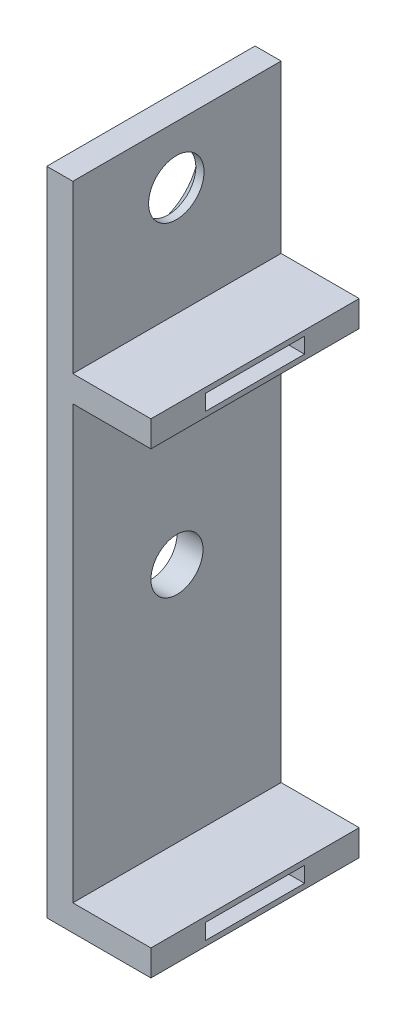
SolidWorks part; units mm, degrees
ref_plane "Front Plane" through (0, 0, 0) normal (0, 0, 1) x (1, 0, 0)
ref_plane "Top Plane" through (0, 0, 0) normal (0, 1, 0) x (1, 0, 0)
ref_plane "Right Plane" through (0, 0, 0) normal (1, 0, 0) x (0, 0, -1)
sketch "Sketch1" plane through (0, 0, 0) normal (0, 0, 1) x (1, 0, 0)
  line L0 (-22.4832, 11.6395) -> (-22.4832, -18.8404)
  line L1 (-22.4832, -18.8404) -> (-18.6732, -18.8404)
  line L2 (-18.6732, -18.8404) -> (-18.6732, -20.1105)
  line L3 (-18.6732, -20.1105) -> (-23.7532, -20.1105)
  line L4 (-23.7532, -20.1105) -> (-23.7532, 11.6395)
  line L5 (-23.7532, 11.6395) -> (-22.4832, 11.6395)
  dimension "D1" = 30.48
  dimension "D2" = 31.75
  dimension "D3" = 5.08
extrude "Boss-Extrude1" add sketch "Sketch1" along normal blind 10.16
sketch "Sketch5" plane through (-18.6732, 0, 0) normal (1, 0, 0) x (0, 0, -1)
  line L0 (-7.493, -19.8565) -> (-2.667, -19.8565)
  line L1 (-2.667, -19.8565) -> (-2.667, -19.0944)
  line L2 (-2.667, -19.0944) -> (-7.493, -19.0944)
  line L3 (-7.493, -19.0944) -> (-7.493, -19.8565)
  line L4 (0, -20.1105) -> (0, -18.8404) construction
  line L5 (-10.16, -20.1105) -> (-10.16, -18.8404) construction
  line L6 (-10.16, -18.8404) -> (0, -18.8404) construction
  line L7 (-10.16, -20.1105) -> (0, -20.1105) construction
  dimension "D1" = 2.667
  dimension "D2" = 2.667
  dimension "D3" = 0.254
  dimension "D4" = 0.254
sketch "Sketch6" plane through (-22.4832, 0, 0) normal (1, 0, 0) x (0, 0, -1)
  line L0 (-10.16, -18.8404) -> (-10.16, 2.2416) construction
  line L1 (-10.16, -18.8404) -> (-10.16, 11.6396) construction
  line L2 (-10.16, 2.2416) -> (0, 2.2416)
  line L3 (0, -18.8404) -> (0, 11.6396) construction
  line L4 (0, 2.2416) -> (0, 3.5116)
  line L5 (0, 3.5116) -> (-10.16, 3.5116)
  line L6 (-10.16, 3.5116) -> (-10.16, 2.2416)
  line L7 (-10.16, -18.8404) -> (0, -18.8404) construction
  dimension "D1" = 1.27
  dimension "D2" = 21.082
extrude "Boss-Extrude3" add sketch "Sketch6" along normal blind 3.81
sketch "Sketch8" plane through (-18.6732, 0, 0) normal (1, 0, 0) x (0, 0, -1)
  line L0 (-7.493, 3.2576) -> (-7.493, 2.4956)
  line L1 (-7.493, 2.4956) -> (-2.667, 2.4956)
  line L2 (-2.667, 2.4956) -> (-2.667, 3.2576)
  line L3 (-2.667, 3.2576) -> (-7.493, 3.2576)
  line L4 (0, 2.2416) -> (0, 3.5116) construction
  line L5 (0, 3.5116) -> (-10.16, 3.5116) construction
  line L6 (-10.16, 2.2416) -> (0, 2.2416) construction
  line L8 (-10.16, 3.5116) -> (-10.16, 2.2416) construction
  dimension "D1" = 2.667
  dimension "D2" = 2.667
  dimension "D3" = 0.254
  dimension "D4" = 0.254
sketch "Sketch11" plane through (-22.4832, 0, 0) normal (1, 0, 0) x (0, 0, -1)
  point P0 (-5.08, -7.0844)
sketch "Sketch14" plane through (-22.4832, 0, 0) normal (1, 0, 0) x (0, 0, -1)
  line L0 (-10.16, 11.6395) -> (0, 11.6395) construction
  point P0 (-5.1117, 8.8455)
  dimension "D1" = 2.794
extrude "Cut-Extrude1" cut sketch "Sketch8" against normal blind 2.2352
extrude "Cut-Extrude2" cut sketch "Sketch5" against normal blind 2.2352
sketch "Sketch17" plane through (-22.4832, 0, 0) normal (1, 0, 0) x (0, 0, -1)
  circle A0 centre (-5.08, -7.0844) radius 1.27
extrude "Cut-Extrude3" cut sketch "Sketch17" against normal blind 2.54
hole_wizard "#6-32 Tapped Hole1" positions "Sketch21" profile "Sketch22" tap size "#6-32" standard "ANSI Inch"
sketch "Sketch21" plane through (-23.7532, 0, 0) normal (-1, 0, 0) x (0, 0, 1)
  point P0 (5.1117, 8.8455)
  point P3 (5.1117, 8.8455)
sketch "Sketch22" plane through (-23.7532, 8.8455, 5.1117) normal (0, 1, 0) x (0, 0, 1)
  line L0 (0, 0) -> (0, 10.2107)
  line L1 (0, 10.2107) -> (1.3525, 9.398)
  line L2 (1.3525, 9.398) -> (1.3525, 0.8685)
  line L3 (1.3525, 0.8685) -> (2.3876, 0)
  line L5 (2.3876, 0) -> (0, 0)
  line L6 (-1.3525, 0.8685) -> (-2.3876, 0) construction
  line L10 (0, 10.2107) -> (-1.3525, 9.398) construction
  line L11 (0, -6.35) -> (0, 107.95) construction
  dimension "Tap Drill Dia." = 2.7051
  dimension "Tap Drill Depth" = 9.398
  dimension "Near C'Sink Dia." = 4.7752
  dimension "Near C'Sink Angle" = 100
  dimension "Drill Angle" = 118
cosmetic thread "Hole Thread5" parameters "D1"=1.27, "D2"=3.5052
cosmetic thread "Hole Thread6" parameters "D1"=1.27, "D2"=3.5052
